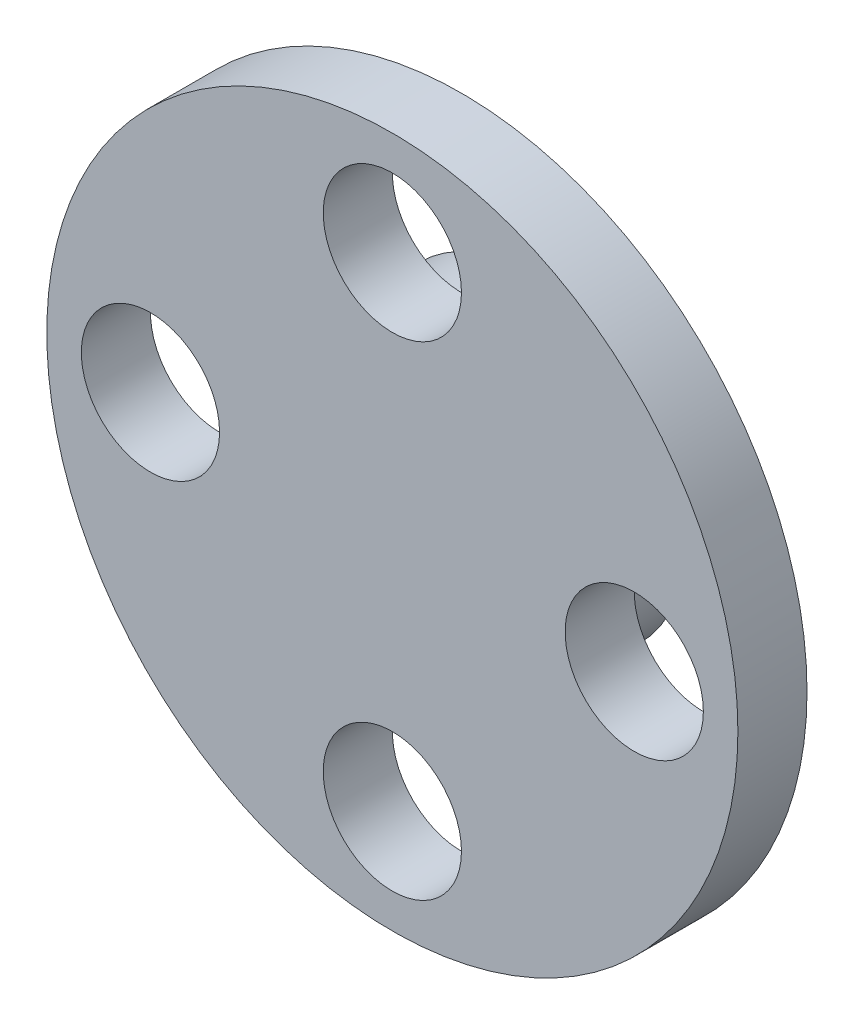
SolidWorks part; units mm, degrees
ref_plane "Front Plane" through (0, 0, 0) normal (0, 0, 1) x (1, 0, 0)
ref_plane "Top Plane" through (0, 0, 0) normal (0, 1, 0) x (1, 0, 0)
ref_plane "Right Plane" through (0, 0, 0) normal (1, 0, 0) x (0, 0, -1)
sketch "Sketch1" plane through (0, 0, 0) normal (0, 0, 1) x (1, 0, 0)
  circle A0 centre (0, 0) radius 10
  circle A1 centre (7, 0) radius 2
  circle A2 centre (0, 7) radius 2
  circle A3 centre (-7, 0) radius 2
  circle A4 centre (0, -7) radius 2
extrude "Boss-Extrude1" add sketch "Sketch1" along normal blind 2
sketch "Sketch2" plane through (0, 0, 0) normal (0, 0, -1) x (-1, 0, 0)
  circle A0 centre (0, 0) radius 4.5
  circle A1 centre (0, 0) radius 3.5
extrude "Boss-Extrude2" add sketch "Sketch2" along normal blind 2
